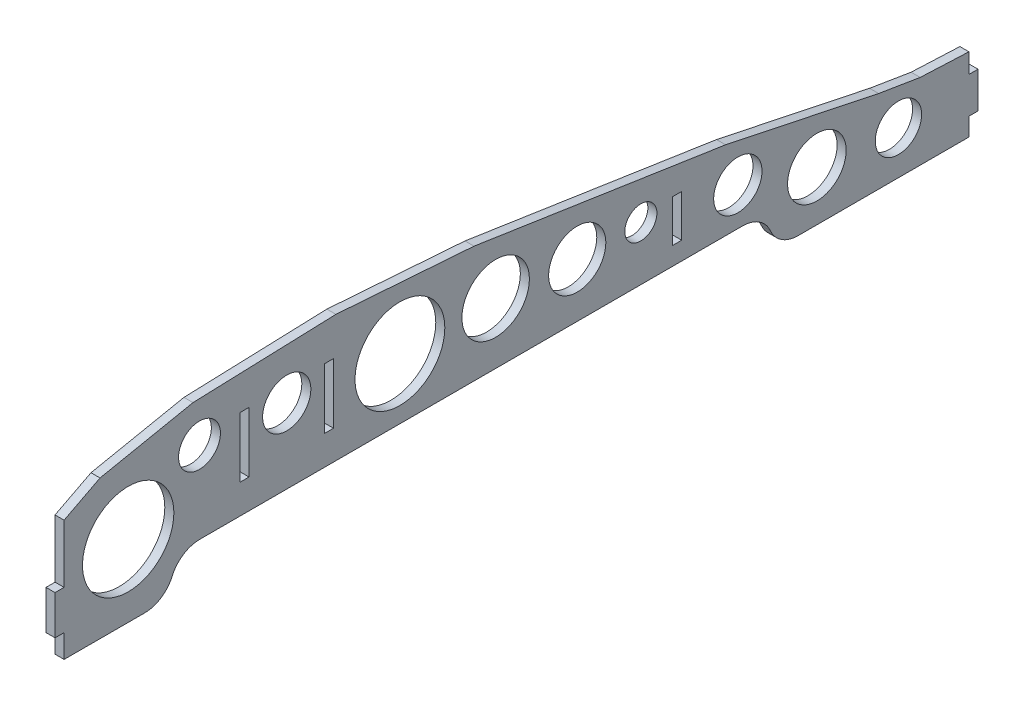
SolidWorks part; units mm, degrees
ref_plane "Front Plane" through (0, 0, 0) normal (0, 0, 1) x (1, 0, 0)
ref_plane "Top Plane" through (0, 0, 0) normal (0, 1, 0) x (1, 0, 0)
ref_plane "Right Plane" through (0, 0, 0) normal (1, 0, 0) x (0, 0, -1)
sketch "Sketch1" plane through (0, 0, 0) normal (1, 0, 0) x (0, 0, -1)
  line L1 (0, 0) -> (11.9108, 6.158)
  line L2 (11.9108, 6.158) -> (42.7394, 12.3835)
  line L3 (42.7394, 12.3835) -> (90.1068, 14.0331)
  line L4 (90.1068, 14.0331) -> (135.8874, 10.7137)
  line L5 (135.8874, 10.7137) -> (219.2875, -1.8767)
  line L6 (219.2875, -1.8767) -> (270.057, -12.5326)
  line L7 (270.057, -12.5326) -> (283.8231, -14.7929)
  line L8 (283.8231, -14.7929) -> (299.9881, -15.5174)
  line L11 (0, 0) -> (-111.4557, 0) construction
  line L12 (0, 0) -> (0, 53.0813) construction
  line L13 (0, 0) -> (0, -40)
  line L14 (0, -40) -> (299.9881, -40)
  line L15 (299.9881, -40) -> (299.9881, -15.5174)
other "AlignGroup1"
other "AlignGroup2" parameters "D1"=38.5383, "D2"=11.9108, "D3"=42.7394, "D4"=90.1068, "D5"=135.8874, "D6"=219.2875, "D7"=270.057, "D8"=283.8231, "D9"=299.9881, "D10"=6.158, "D11"=10.7137, "D12"=12.3835, "D13"=14.0331, "D14"=1.8767, "D15"=12.5326, "D16"=14.7929, "D17"=15.5174, "D18"=59.1305
extrude "Boss-Extrude1" add sketch "Sketch1" along normal blind 3
sketch "Sketch2" plane through (3, 0, 0) normal (1, 0, 0) x (0, 0, -1)
  line L0 (35, -40) -> (35, -38)
  line L1 (0, -40) -> (299.9881, -40) construction
  line L2 (45, -28) -> (225, -28)
  line L3 (235, -38) -> (235, -40)
  line L4 (235, -40) -> (35, -40)
  line L5 (0, 0) -> (0, -40) construction
  arc A0 (225, -28) -> (235, -38) centre (225, -38) cw
  arc A1 (35, -38) -> (45, -28) centre (45, -38) cw
  point P10 (235, -28)
  point P13 (35, -28)
  dimension "D4" = 10
  dimension "D1" = 200
  dimension "D2" = 35
  dimension "D3" = 12
extrude "Cut-Extrude1" cut sketch "Sketch2" against normal blind 3
fillet "Fillet1" radius 10 2 edges at (1.5, -40, -235) (1.5, -40, -35)
sketch "Sketch3" plane through (3, 0, 0) normal (1, 0, 0) x (0, 0, -1)
  line L2 (0, -40) -> (26.6697, -40) construction
  line L3 (0, 0) -> (0, -40) construction
  circle A0 centre (73.81, -3.27) radius 8
  dimension "D1" = 36.73
  dimension "D2" = 16
  dimension "D3" = 73.81
extrude "Cut-Extrude2" cut sketch "Sketch3" against normal blind 3
sketch "Sketch5" plane through (3, 0, 0) normal (1, 0, 0) x (0, 0, -1)
  line L0 (0, 0) -> (0, -40) construction
  line L1 (0, -19.3) -> (-3, -19.3)
  line L2 (0, -19.3) -> (0, -32.3)
  line L3 (0, -32.3) -> (-3, -32.3)
  line L4 (-3, -19.3) -> (-3, -32.3)
  line L5 (299.9881, -40) -> (299.9881, -15.5174) construction
  line L6 (299.9881, -22.0174) -> (302.9881, -22.0174)
  line L7 (299.9881, -22.0174) -> (299.9881, -34.0174)
  line L8 (299.9881, -34.0174) -> (302.9881, -34.0174)
  line L9 (302.9881, -22.0174) -> (302.9881, -34.0174)
  dimension "D1" = 3
  dimension "D2" = 6.5
  dimension "D3" = 12
  dimension "D4" = 19.3
  dimension "D5" = 13
  dimension "D6" = 3
extrude "Boss-Extrude2" add sketch "Sketch5" against normal up to surface (3 mm away) up to face at (0, -3.27, -81.81)
sketch "Sketch6" plane through (3, 0, 0) normal (1, 0, 0) x (0, 0, -1)
  line L0 (0, 0) -> (0, -19.3) construction
  line L1 (58.31, 1.73) -> (61.31, 1.73)
  line L2 (58.31, 1.73) -> (58.31, -18.27)
  line L3 (58.31, -18.27) -> (61.31, -18.27)
  line L4 (61.31, 1.73) -> (61.31, -18.27)
  line L5 (86.31, 1.73) -> (89.31, 1.73)
  line L6 (86.31, 1.73) -> (86.31, -18.27)
  line L7 (86.31, -18.27) -> (89.31, -18.27)
  line L8 (89.31, 1.73) -> (89.31, -18.27)
  line L9 (201.745, -8) -> (204.745, -8)
  line L10 (201.745, -8) -> (201.745, -22)
  line L11 (201.745, -22) -> (204.745, -22)
  line L12 (204.745, -8) -> (204.745, -22)
  line L13 (225, -28) -> (45, -28) construction
  circle A0 centre (21.2423, -16.0718) radius 15.1477
  circle A1 centre (44.8841, -0.9241) radius 6.9404
  circle A2 centre (111.3366, -7.8645) radius 14.8862
  circle A3 centre (143.0719, -7.8645) radius 11.1859
  circle A4 centre (170.1215, -10.1081) radius 9.4781
  circle A5 centre (191.2074, -10.1081) radius 5.3247
  circle A6 centre (223.3687, -15.4328) radius 8.0086
  circle A7 centre (249.5663, -23.4414) radius 9.7125
  circle A8 centre (276.6159, -25.6563) radius 7.6872
  dimension "D1" = 3
  dimension "D2" = 58.31
  dimension "D3" = 86.31
  dimension "D4" = 9.73
  dimension "D5" = 20
  dimension "D6" = 201.745
  dimension "D7" = 6
  dimension "D8" = 14
extrude "Cut-Extrude3" cut sketch "Sketch6" against normal blind 10
